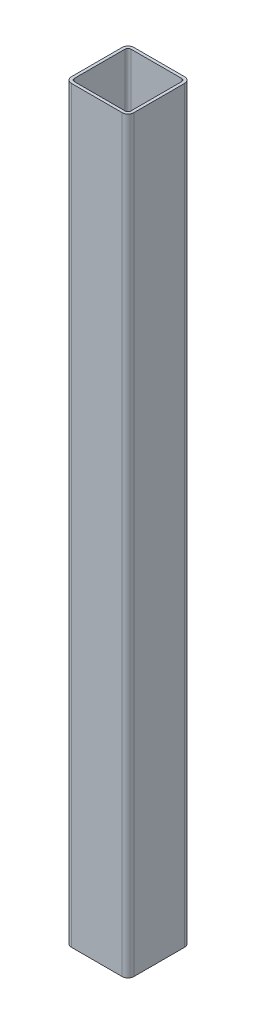
SolidWorks part; units mm, degrees
ref_plane "Front Plane" through (0, 0, 0) normal (0, 0, 1) x (1, 0, 0)
ref_plane "Top Plane" through (0, 0, 0) normal (0, 1, 0) x (1, 0, 0)
ref_plane "Right Plane" through (0, 0, 0) normal (1, 0, 0) x (0, 0, -1)
sketch "Sketch1" plane through (0, 0, 0) normal (0, 1, 0) x (1, 0, 0)
  line L0 (-41.275, -46.0375) -> (41.275, -46.0375)
  line L1 (-46.0375, -41.275) -> (-46.0375, 41.275)
  line L2 (41.275, 46.0375) -> (-41.275, 46.0375)
  line L3 (46.0375, 41.275) -> (46.0375, -41.275)
  line L4 (-41.275, -50.8) -> (41.275, -50.8)
  line L5 (-50.8, -41.275) -> (-50.8, 41.275)
  line L6 (41.275, 50.8) -> (-41.275, 50.8)
  line L7 (50.8, 41.275) -> (50.8, -41.275)
  line L10 (-46.0375, 0) -> (46.0375, 0) construction
  arc A0 (50.8, 41.275) -> (41.275, 50.8) centre (41.275, 41.275) ccw
  arc A1 (41.275, -50.8) -> (50.8, -41.275) centre (41.275, -41.275) ccw
  arc A2 (-50.8, -41.275) -> (-41.275, -50.8) centre (-41.275, -41.275) ccw
  arc A3 (-41.275, 50.8) -> (-50.8, 41.275) centre (-41.275, 41.275) ccw
  arc A4 (-41.275, 46.0375) -> (-46.0375, 41.275) centre (-41.275, 41.275) ccw
  arc A5 (46.0375, 41.275) -> (41.275, 46.0375) centre (41.275, 41.275) ccw
  arc A6 (41.275, -46.0375) -> (46.0375, -41.275) centre (41.275, -41.275) ccw
  arc A7 (-46.0375, -41.275) -> (-41.275, -46.0375) centre (-41.275, -41.275) ccw
extrude "Boss-Extrude1" add sketch "Sketch1" along normal mid plane 1219.2
